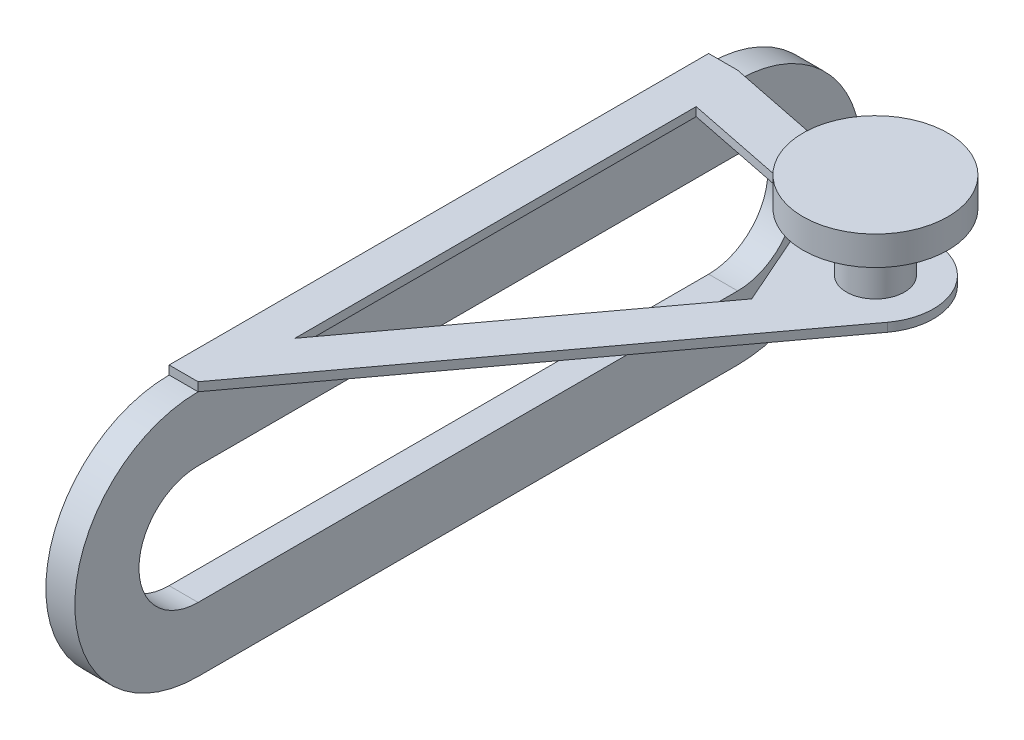
SolidWorks part; units mm, degrees
material "1060 Alloy"
ref_plane "Front Plane" through (0, 0, 0) normal (0, 0, 1) x (1, 0, 0)
ref_plane "Top Plane" through (0, 0, 0) normal (0, 1, 0) x (1, 0, 0)
ref_plane "Right Plane" through (0, 0, 0) normal (1, 0, 0) x (0, 0, -1)
ref_plane "Plane1" through (0, 0, 0) normal (-1, 0, 0) x (0, -1, 0)
sketch "Sketch1" plane through (0, 0, 0) normal (-1, 0, 0) x (0, -1, 0)
  line L0 (-42.5, 186) -> (-42.5, 0)
  line L1 (42.5, 0) -> (42.5, 186)
  arc A0 (-42.5, 0) -> (42.5, 0) centre (0, 0) ccw
  arc A1 (42.5, 186) -> (-42.5, 186) centre (0, 186) ccw
extrude "Boss-Extrude1" add sketch "Sketch1" against normal blind 10
sketch "Sketch2" plane through (0, 42.5, 0) normal (0, 1, 0) x (-1, 0, 0)
  line L0 (-10, 0) -> (-98.9444, 17.8928)
  line L1 (-111.0774, 49.3961) -> (-10, 186)
  line L2 (-10, 186) -> (0, 186)
  line L3 (0, 186) -> (0, 0)
  line L4 (0, 0) -> (-10, 0)
  arc A0 (-98.9444, 17.8928) -> (-111.0774, 49.3961) centre (-95, 37.5) cw
extrude "Boss-Extrude2" add sketch "Sketch2" along normal blind 3
sketch "Sketch3" plane through (0, 45.5, 0) normal (0, 1, 0) x (-1, 0, 0)
  circle A0 centre (-95, 37.5) radius 10
extrude "Boss-Extrude3" add sketch "Sketch3" along normal blind 20
sketch "Sketch4" plane through (10, 0, 0) normal (1, 0, 0) x (0, 0, -1)
  line L0 (0, 20.39) -> (-186, 20.39)
  line L1 (-186, -20.39) -> (0, -20.39)
  arc A0 (-186, 20.39) -> (-186, -20.39) centre (-186, 0) ccw
  arc A1 (0, -20.39) -> (0, 20.39) centre (0, 0) ccw
extrude "Cut-Extrude1" cut sketch "Sketch4" against normal through all
sketch "Sketch5" plane through (0, 45.5, 0) normal (0, 1, 0) x (-1, 0, 0)
  line L0 (-64.1029, 28.1523) -> (-13.7159, 18.016)
  line L1 (-13.7159, 18.016) -> (-13.7159, 156.3592)
  line L2 (-13.7159, 156.3592) -> (-80.693, 65.8412)
  line L3 (-80.693, 65.8412) -> (-64.1029, 28.1523)
extrude "Cut-Extrude2" cut sketch "Sketch5" against normal through all
sketch "Sketch6" plane through (0, 65.5, 0) normal (0, 1, 0) x (1, 0, 0)
  circle A0 centre (95, -37.5) radius 25
extrude "Boss-Extrude4" add sketch "Sketch6" along normal blind 10
